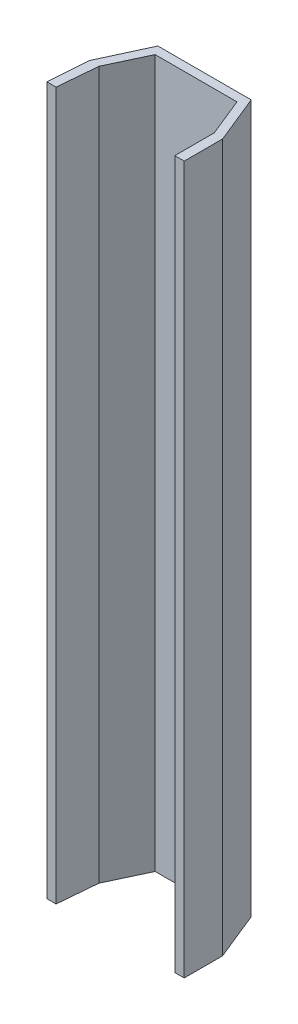
SolidWorks part; units mm, degrees
ref_plane "Front Plane" through (0, 0, 0) normal (0, 0, 1) x (1, 0, 0)
ref_plane "Top Plane" through (0, 0, 0) normal (0, 1, 0) x (1, 0, 0)
ref_plane "Right Plane" through (0, 0, 0) normal (1, 0, 0) x (0, 0, -1)
sketch "Sketch1" plane through (0, 0, 0) normal (0, 1, 0) x (1, 0, 0)
  line L0 (0, 0) -> (1.2255, 14.1613)
  line L1 (1.2255, 14.1613) -> (7.6599, 27.8944)
  line L2 (7.6599, 27.8944) -> (37.0469, 27.8944)
  line L3 (37.0469, 27.8944) -> (42.617, 14.1613)
  line L4 (42.617, 14.1613) -> (42.617, 0)
  line L5 (0, 0) -> (-3.3348, 0)
  line L6 (-3.3348, 0) -> (-2.3164, 14.1613)
  line L7 (-2.3164, 14.1613) -> (5.4939, 31.0596)
  line L8 (5.4939, 31.0596) -> (38.9969, 31.0596)
  line L9 (38.9969, 31.0596) -> (46.0031, 13.7856)
  line L10 (46.0031, 13.7856) -> (46.0031, 0)
  line L11 (46.0031, 0) -> (42.617, 0)
  point P7 (-3.3348, 0)
extrude "Boss-Extrude1" add sketch "Sketch1" along normal blind 254
